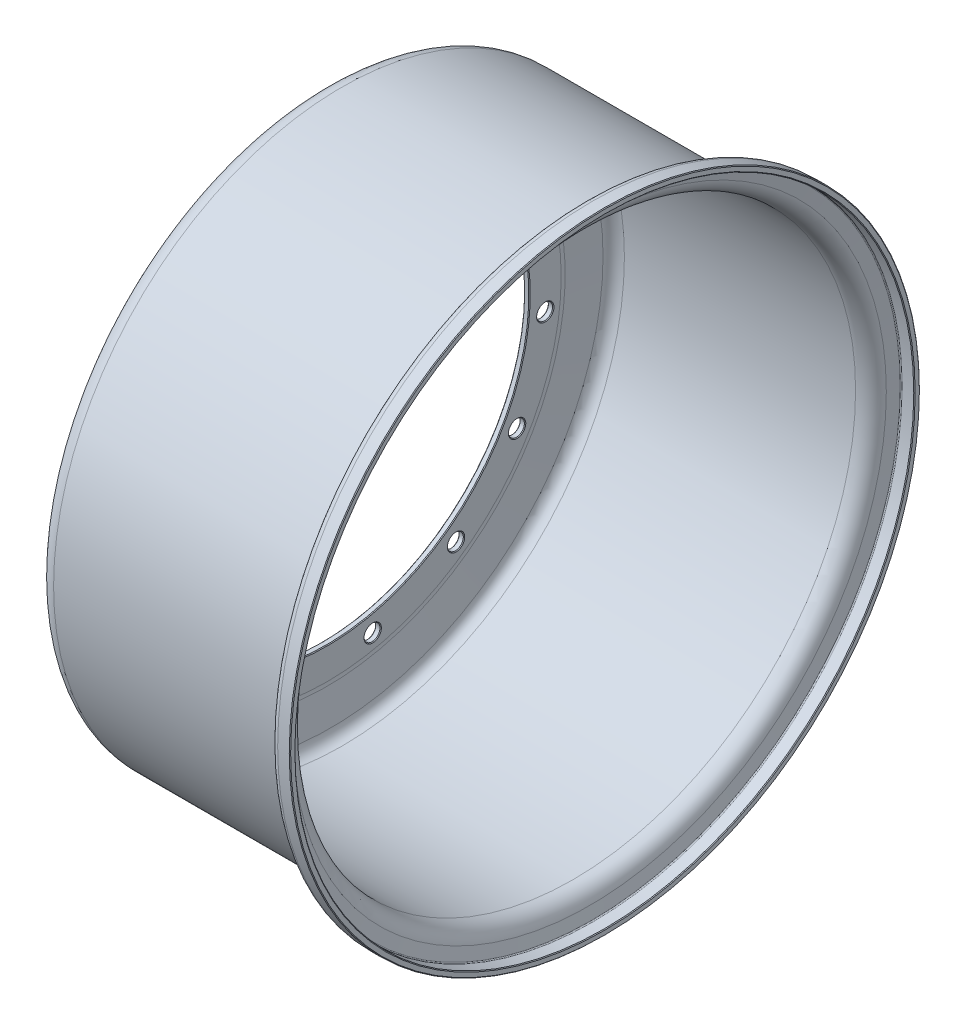
SolidWorks part; units mm, degrees
material "6061-T6 (SS)"
ref_plane "Front Plane" through (0, 0, 0) normal (0, 0, 1) x (1, 0, 0)
ref_plane "Top Plane" through (0, 0, 0) normal (0, 1, 0) x (1, 0, 0)
ref_plane "Right Plane" through (0, 0, 0) normal (1, 0, 0) x (0, 0, -1)
ref_axis "Axis1" through (-6.731, 0, 0) along (1, 0, 0)
sketch "Sketch1" plane through (0, 0, 0) normal (0, 0, 1) x (1, 0, 0)
  line L0 (0, -55) -> (0, 55) construction
  line L1 (0, 114.3) -> (0, 132.1206)
  line L2 (0.1187, 134.574) -> (2.0071, 154.0431)
  line L3 (3.175, 114.3) -> (3.175, 132.1206)
  line L4 (11.4879, 162.6489) -> (141.9449, 162.6489)
  line L5 (148.2075, 167.9487) -> (149.3262, 174.6196)
  line L6 (153.0838, 177.7995) -> (160.0206, 177.7995)
  line L7 (3.2789, 134.2674) -> (5.1673, 153.7366)
  line L8 (11.4879, 159.4739) -> (141.9449, 159.4739)
  line L9 (151.3388, 167.4236) -> (152.4575, 174.0945)
  line L10 (153.0838, 174.6245) -> (160.0206, 174.6245)
  line L11 (160.0206, 177.7995) -> (160.0206, 174.6245)
  line L12 (0, 114.3) -> (3.175, 114.3)
  arc A0 (0, 132.1206) -> (0.1187, 134.574) centre (25.4122, 132.1206) cw
  arc A1 (2.0071, 154.0431) -> (11.4879, 162.6489) centre (11.4879, 153.1235) cw
  arc A2 (141.9449, 162.6489) -> (148.2075, 167.9487) centre (141.9449, 168.999) ccw
  arc A3 (149.3262, 174.6196) -> (153.0838, 177.7995) centre (153.0838, 173.9894) cw
  arc A4 (3.175, 132.1206) -> (3.2789, 134.2674) centre (25.4122, 132.1206) cw
  arc A5 (5.1673, 153.7366) -> (11.4879, 159.4739) centre (11.4879, 153.1235) cw
  arc A6 (141.9449, 159.4739) -> (151.3388, 167.4236) centre (141.9449, 168.999) ccw
  arc A7 (152.4575, 174.0945) -> (153.0838, 174.6245) centre (153.0838, 173.9894) cw
  dimension "D4" = 2.4562
  dimension "D2" = 114.3
  dimension "D3" = 174.46
  dimension "D5" = 17.8206
  dimension "D6" = 19.5605
  dimension "D7" = 12.8041
  dimension "D8" = 130.4569
  dimension "D9" = 8.2042
  dimension "D10" = 6.764
  dimension "D11" = 99.52
  dimension "D12" = 4.9225
  dimension "D13" = 6.9367
  dimension "D14" = 3.175
revolve "Outer Rim" add sketch "Sketch1" angle 360 about axis through (-6.731, 0, 0) along (1, 0, 0)
sketch "Sketch2" plane through (0, 0, 0) normal (-1, 0, 0) x (0, 0, 1)
  circle A0 centre (0, 123.825) radius 4.4983
  circle A1 centre (0, 0) radius 114.3 construction
  dimension "D2" = 8.9967
  dimension "D1" = 9.525
extrude "Mounting Hole" cut sketch "Sketch2" against normal through all
pattern_circular "Mounting Hole Pattern" count 15 over 360 about axis through (0, 0, 0) along (1, 0, 0) of "Mounting Hole"
chamfer "Edge Chamfer" distance 0.3962 angle 45 34 edges at (3.175, 0, 114.3) (3.175, 123.825, 4.4983) (3.175, 113.1198, 54.8625) (3.175, 82.8551, 96.5182) (3.175, 38.264, 122.2629) (3.175, -12.9432, 127.645) (3.175, -61.9125, 111.7339) (3.175, -100.1765, 77.2808) (3.175, -121.1191, 30.243) (3.175, -121.1191, -21.2463) (3.175, -100.1765, -68.2842) (3.175, -61.9125, -102.7373) (3.175, -12.9432, -118.6483) (3.175, 38.264, -113.2662) (3.175, 82.8551, -87.5216) (3.175, 113.1198, -45.8658) (0, 0, 114.3) (0, 123.825, 4.4983) (0, 111.2901, 54.4736) (0, 79.5122, 95.0299) (0, 33.9859, 119.1546) (0, -17.4169, 122.6765) (0, -65.8082, 104.9864) (0, -102.8206, 69.1433) (0, -122.0544, 21.3446) (0, -120.1839, -30.1447) (0, -97.5325, -76.4217) (0, -58.0168, -109.4848) (0, -8.4695, -123.6169) (0, 42.5422, -116.3745) (0, 86.198, -89.0099) (0, 114.9494, -46.2547) (160.0206, 0, 174.6245) (160.0206, 0, 177.7995)
